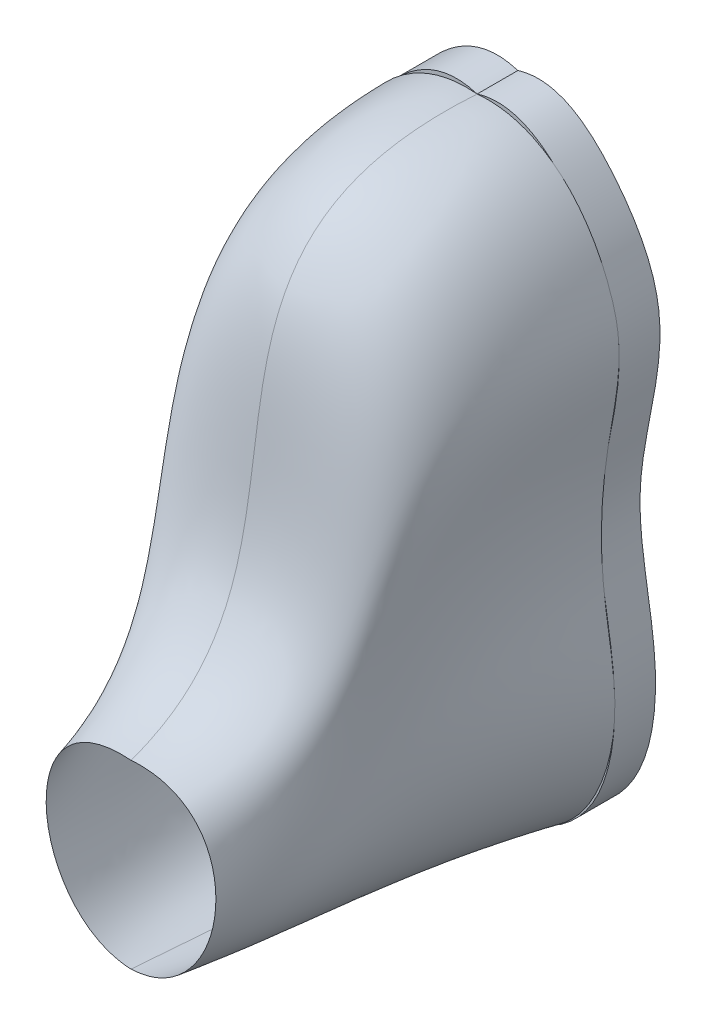
SolidWorks part; units mm, degrees
ref_plane "Front Plane" through (0, 0, 0) normal (0, 0, 1) x (1, 0, 0)
ref_plane "Top Plane" through (0, 0, 0) normal (0, 1, 0) x (1, 0, 0)
ref_plane "Right Plane" through (0, 0, 0) normal (1, 0, 0) x (0, 0, -1)
sketch "Sketch2" plane through (0, 0, 0) normal (0, 0, 1) x (1, 0, 0)
  spline S0 degree 3 poles (0, 99.1833) (9.9401, 102.2623) (24.1226, 90.4641) (40.3345, 61.9432) (25.18, 26.4363) (39.0472, -17.7172) (27.2802, -52.0991) (0, -50.8167) knots 0 0 0 0 0.146529 0.268877 0.50326 0.69401 1 1 1 1
  spline S1 degree 3 poles (0, 99.1833) (-9.9401, 102.2623) (-24.1226, 90.4641) (-40.3345, 61.9432) (-25.18, 26.4363) (-39.0472, -17.7172) (-27.2802, -52.0991) (0, -50.8167) knots 0 0 0 0 0.146529 0.268877 0.50326 0.69401 1 1 1 1
extrude "Boss-Extrude1" add sketch "Sketch2" along normal blind 10
ref_plane "Plane1" through (0, 0, 10) normal (0, 0, 1) x (1, 0, 0)
sketch "Sketch3" plane through (0, 0, 10) normal (0, 0, 1) x (1, 0, 0)
  spline S0 degree 3 poles (0, 99.1833) (-17.1467, 100.6984) (-29.7135, 85.2596) (-36.3506, 60.1853) (-30.961, 39.1158) (-29.5324, 10.3923) (-37.1307, -19.0046) (-24.8521, -49.0317) (-5.9362, -51.0729) (0, -50.8167) knots 0 0 0 0 0.244049 0.265991 0.413933 0.57758 0.721998 0.901928 1 1 1 1
  spline S1 degree 3 poles (0, 99.1833) (-9.9401, 102.2623) (-24.1226, 90.4641) (-40.3345, 61.9432) (-25.18, 26.4363) (-39.0472, -17.7172) (-27.2802, -52.0991) (0, -50.8167) knots 0 0 0 0 0.146529 0.268877 0.50326 0.69401 1 1 1 1 construction
  spline S2 degree 3 poles (0, 99.1833) (17.1467, 100.6984) (29.7135, 85.2596) (36.3506, 60.1853) (30.961, 39.1158) (29.5324, 10.3923) (37.1307, -19.0046) (24.8521, -49.0317) (5.9362, -51.0729) (0, -50.8167) knots 0 0 0 0 0.244049 0.265991 0.413933 0.57758 0.721998 0.901928 1 1 1 1
ref_plane "Plane2" through (0, 0, 95) normal (0, 0, 1) x (1, 0, 0)
sketch "Sketch4" plane through (0, 0, 95) normal (0, 0, 1) x (1, 0, 0)
  spline S0 degree 3 poles (0, 0) (-18.9282, 1.3946) (-26.9108, -26.2332) (-9.3887, -44.1012) (0, -44.4111) knots 0 0 0 0 0.600416 1 1 1 1
  spline S1 degree 3 poles (0, 0) (18.9282, 1.3946) (26.9108, -26.2332) (9.3887, -44.1012) (0, -44.4111) knots 0 0 0 0 0.600416 1 1 1 1
sketch3d "3DSketch7"
  spline S0 degree 3 poles (-2.5038, 99.2949, 10) (-0.6148, 105.9831, 95.6811) (-5.8284, 14.3509, 34.7698) (0, 0, 95) knots 0 0 0 0 1 1 1 1
  spline S1 degree 3 poles (0, 99.1833, 10) (-17.1467, 100.6984, 10) (-29.7135, 85.2596, 10) (-36.3506, 60.1853, 10) (-30.961, 39.1158, 10) (-29.5324, 10.3923, 10) (-37.1307, -19.0046, 10) (-24.8521, -49.0317, 10) (-5.9362, -51.0729, 10) (0, -50.8167, 10) knots 0 0 0 0 0.244049 0.265991 0.413933 0.57758 0.721998 0.901928 1 1 1 1 construction
sketch3d "3DSketch8"
  spline S0 degree 1 poles (0, -50.8167, 10) (0, -44.4111, 95) knots 0 0 1 1
  spline S1 degree 1 poles (9.8039, -41.2392, 95) (17.9339, -47.4274, 10) knots 0 0 1 1
  spline S2 degree 1 poles (-9.8039, -41.2392, 95) (-17.9339, -47.4274, 10) knots 0 0 1 1
surface "Surface-Loft2"
